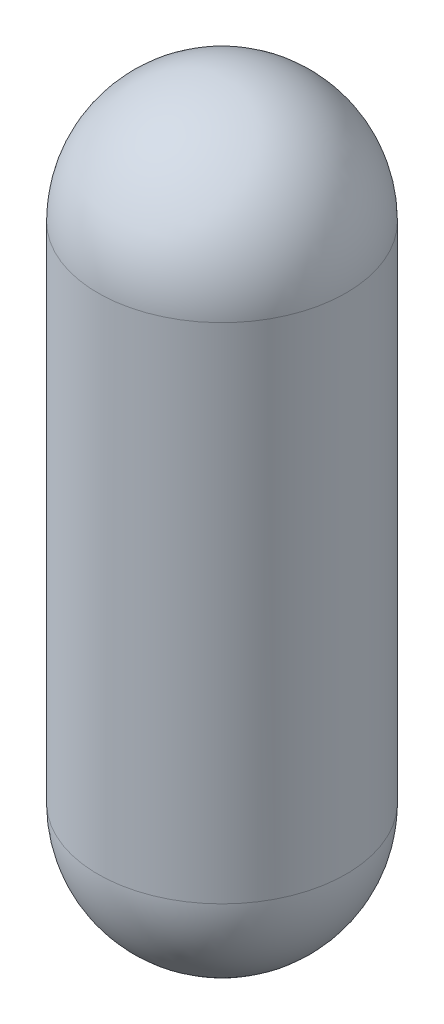
SolidWorks part; units mm, degrees
material "Titanium"
ref_plane "Front Plane" through (0, 0, 0) normal (0, 0, 1) x (1, 0, 0)
ref_plane "Top Plane" through (0, 0, 0) normal (0, 1, 0) x (1, 0, 0)
ref_plane "Right Plane" through (0, 0, 0) normal (1, 0, 0) x (0, 0, -1)
sketch "Sketch1" plane through (0, 0, 0) normal (0, 0, 1) x (1, 0, 0)
  line L0 (0, 1667.26) -> (0, 1669.8)
  line L2 (0, 0) -> (0, 1339.6) construction
  line L4 (330.2, 0) -> (330.2, 1339.6)
  line L5 (0, -330.2) -> (0, -327.66)
  line L6 (0, 976.2421) -> (330.2, 976.2421) construction
  line L7 (327.66, 1339.6) -> (327.66, 0)
  line L8 (327.66, 319.1286) -> (330.2, 319.1286) construction
  arc A2 (330.2, 1339.6) -> (0, 1669.8) centre (0, 1339.6) ccw
  arc A3 (0, -330.2) -> (330.2, 0) centre (0, 0) ccw
  arc A4 (327.66, 1339.6) -> (0, 1667.26) centre (0, 1339.6) ccw
  arc A5 (327.66, 0) -> (0, -327.66) centre (0, 0) cw
  dimension "D3" = 2.54
  dimension "D4" = 330.2
  dimension "D5" = 327.66
  dimension "D6" = 327.66
  dimension "D1" = 2000
  dimension "D2" = 330.2
revolve "Revolve1" add sketch "Sketch1" angle 360 about L2
